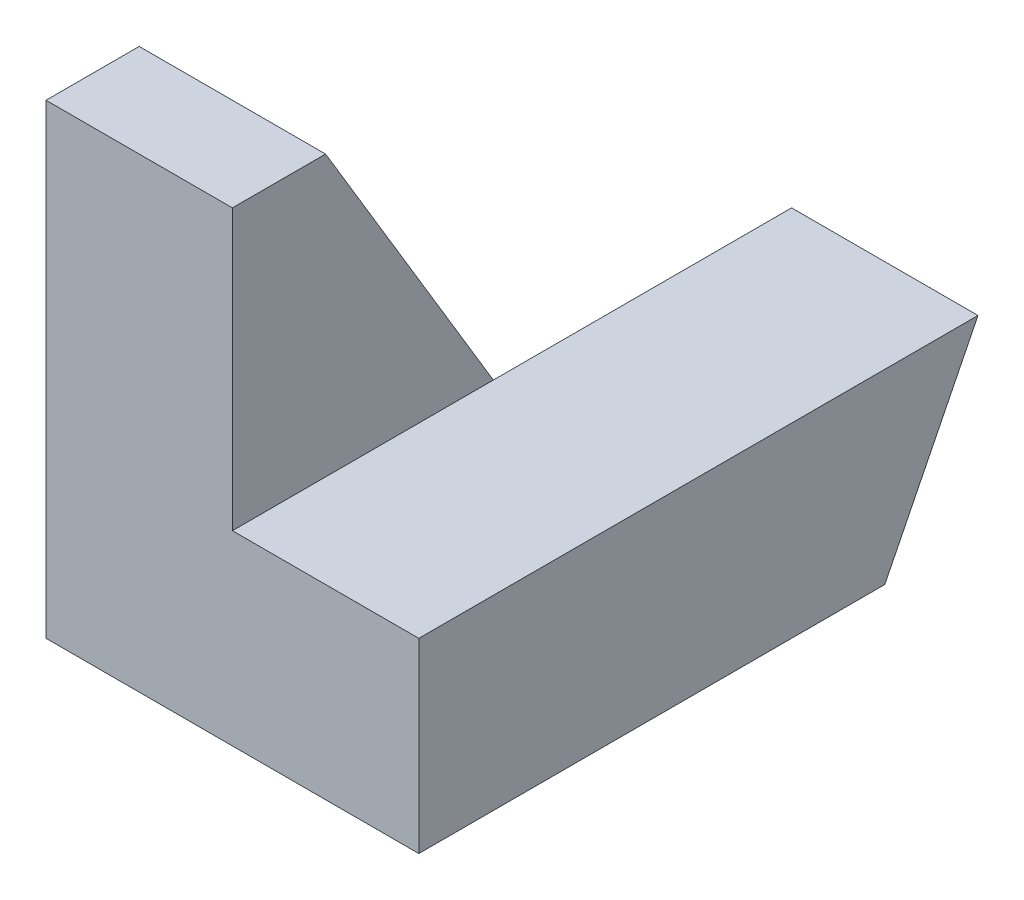
SolidWorks part; units mm, degrees
ref_plane "Front Plane" through (0, 0, 0) normal (0, 0, 1) x (1, 0, 0)
ref_plane "Top Plane" through (0, 0, 0) normal (0, 1, 0) x (1, 0, 0)
ref_plane "Right Plane" through (0, 0, 0) normal (1, 0, 0) x (0, 0, -1)
sketch "Sketch1" plane through (0, 0, 0) normal (1, 0, 0) x (0, 0, -1)
  line L0 (0, 0) -> (0, 5)
  line L1 (0, 5) -> (1, 5)
  line L2 (1, 5) -> (4, 0)
  line L3 (4, 0) -> (0, 0)
  dimension "D1" = 4
  dimension "D2" = 1
  dimension "D3" = 5
extrude "Boss-Extrude1" add sketch "Sketch1" along normal blind 2
sketch "Sketch2" plane through (2, 0, 0) normal (1, 0, 0) x (0, 0, -1)
  line L0 (0, 0) -> (5, 0)
  line L1 (5, 0) -> (6, 2)
  line L2 (6, 2) -> (0, 2)
  line L3 (0, 5) -> (0, 0) construction
  line L4 (0, 2) -> (0, 0)
  dimension "D1" = 2
  dimension "D2" = 5
  dimension "D3" = 6
extrude "Boss-Extrude2" add sketch "Sketch2" along normal blind 2
